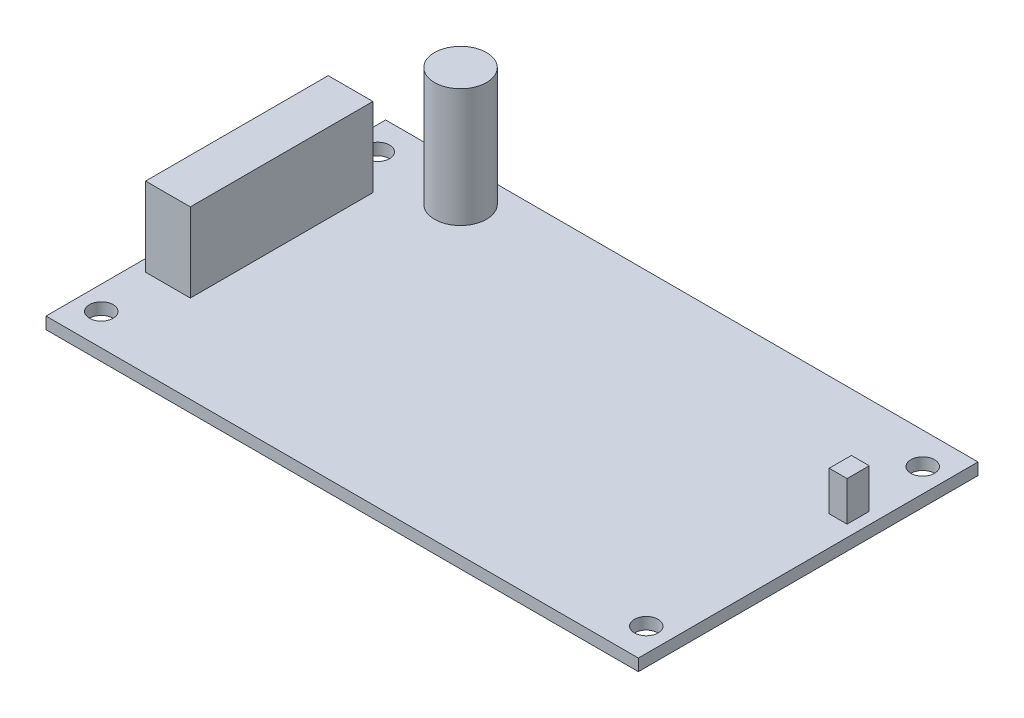
SolidWorks part; units mm, degrees
ref_plane "Front Plane" through (0, 0, 0) normal (0, 0, 1) x (1, 0, 0)
ref_plane "Top Plane" through (0, 0, 0) normal (0, 1, 0) x (1, 0, 0)
ref_plane "Right Plane" through (0, 0, 0) normal (1, 0, 0) x (0, 0, -1)
sketch "Sketch1" plane through (0, 0, 0) normal (0, 1, 0) x (1, 0, 0)
  line L1 (37.5, -21.5) -> (-37.5, -21.5)
  line L2 (37.5, -21.5) -> (37.5, 21.5)
  line L3 (37.5, 21.5) -> (-37.5, 21.5)
  line L4 (-37.5, -21.5) -> (-37.5, 21.5)
  line L5 (37.5, -21.5) -> (-37.5, 21.5) construction
  line L6 (37.5, 21.5) -> (-37.5, -21.5) construction
  line L7 (34.5, -17.5) -> (-34.5, -17.5) construction
  line L8 (34.5, -17.5) -> (34.5, 17.5) construction
  line L9 (34.5, 17.5) -> (-34.5, 17.5) construction
  line L10 (-34.5, -17.5) -> (-34.5, 17.5) construction
  line L11 (34.5, -17.5) -> (-34.5, 17.5) construction
  line L12 (34.5, 17.5) -> (-34.5, -17.5) construction
  circle A0 centre (-34.5, 17.5) radius 1.5
  circle A1 centre (-34.5, -17.5) radius 1.5
  circle A2 centre (34.5, -17.5) radius 1.5
  circle A3 centre (34.5, 17.5) radius 1.5
  point P0 (0, 0)
  point P6 (0, 0)
  dimension "D5" = 3
  dimension "D1" = 75
  dimension "D2" = 43
  dimension "D3" = 69
  dimension "D4" = 35
extrude "Boss-Extrude1" add sketch "Sketch1" along normal blind 1.5
sketch "Sketch3" plane through (0, 1.5, 0) normal (0, 1, 0) x (1, 0, 0)
  line L1 (-35.9946, 12.7222) -> (-30.3317, 12.7222)
  line L2 (-35.9946, 12.7222) -> (-35.9946, -10.395)
  line L3 (-35.9946, -10.395) -> (-30.3317, -10.395)
  line L4 (-30.3317, 12.7222) -> (-30.3317, -10.395)
extrude "Boss-Extrude2" add sketch "Sketch3" along normal blind 10
sketch "Sketch4" plane through (0, 1.5, 0) normal (0, 1, 0) x (1, 0, 0)
  line L1 (33.7731, 9.1975) -> (36.0335, 9.1975)
  line L2 (33.7731, 9.1975) -> (33.7731, 6.3915)
  line L3 (33.7731, 6.3915) -> (36.0335, 6.3915)
  line L4 (36.0335, 9.1975) -> (36.0335, 6.3915)
extrude "Boss-Extrude3" add sketch "Sketch4" along normal blind 5
sketch "Sketch5" plane through (0, 1.5, 0) normal (0, 1, 0) x (1, 0, 0)
  circle A0 centre (-23.5051, 16.9888) radius 3.2921
extrude "Boss-Extrude4" add sketch "Sketch5" along normal blind 15
